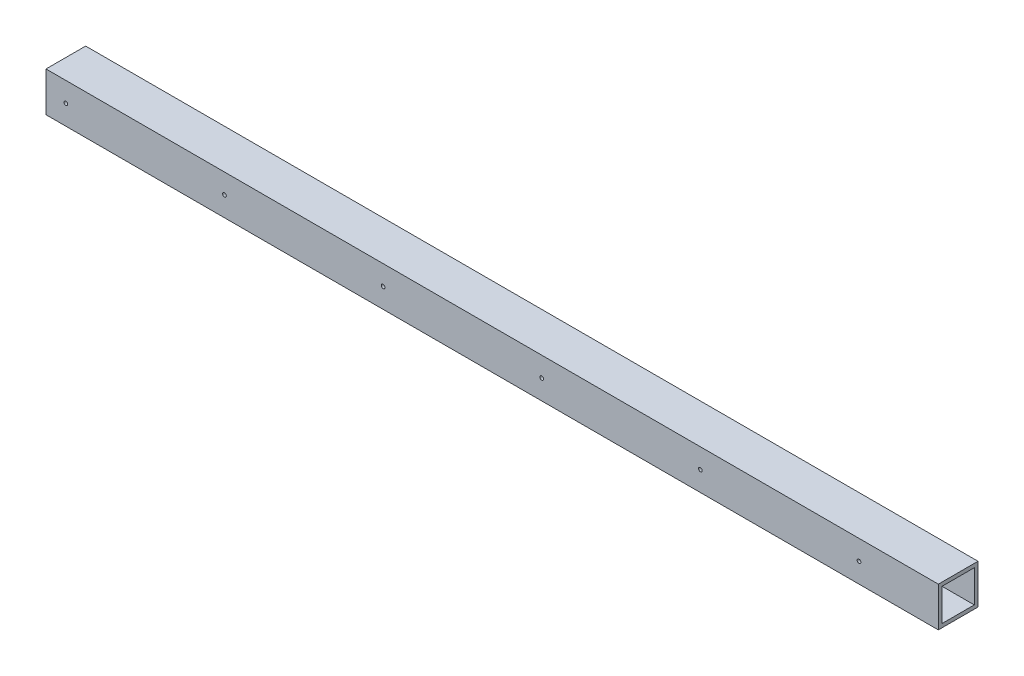
SolidWorks part; units mm, degrees
ref_plane "Front Plane" through (0, 0, 0) normal (0, 0, 1) x (1, 0, 0)
ref_plane "Top Plane" through (0, 0, 0) normal (0, 1, 0) x (1, 0, 0)
ref_plane "Right Plane" through (0, 0, 0) normal (1, 0, 0) x (0, 0, -1)
sketch "Sketch1" plane through (0, 0, 0) normal (1, 0, 0) x (0, 0, -1)
  line L0 (4.7625, 4.7625) -> (4.7625, 46.0375)
  line L1 (0, 0) -> (50.8, 0)
  line L2 (0, 0) -> (0, 50.8)
  line L3 (0, 50.8) -> (50.8, 50.8)
  line L4 (50.8, 0) -> (50.8, 50.8)
  line L5 (4.7625, 46.0375) -> (46.0375, 46.0375)
  line L6 (46.0375, 4.7625) -> (46.0375, 46.0375)
  line L7 (4.7625, 4.7625) -> (46.0375, 4.7625)
  dimension "D1" = 50.8
  dimension "D2" = 4.7625
extrude "Boss-Extrude1" add sketch "Sketch1" along normal blind 1143
sketch "Sketch2" plane through (0, 0, -50.8) normal (0, 0, -1) x (-1, 0, 0)
  line L0 (-1143, 0) -> (-1143, 50.8) construction
  line L1 (-1143, 50.8) -> (0, 50.8) construction
  circle A0 centre (-1041.4, 25.4) radius 2.3813
  dimension "D3" = 4.7625
  dimension "D1" = 101.6
  dimension "D2" = 25.4
extrude "Cut-Extrude1" cut sketch "Sketch2" against normal through all
pattern_linear "LPattern1" count 6 spacing 203.2 along (-1, 0, 0) of "Cut-Extrude1"
sketch "Sketch3" plane through (0, 0, 0) normal (0, -1, 0) x (1, 0, 0)
  line L0 (0, 0) -> (0, -50.8) construction
  circle A0 centre (101.6, -25.4) radius 2.3813
  point P5 (0, -25.4)
  dimension "D1" = 101.6
  dimension "D2" = 4.7625
extrude "Cut-Extrude2" cut sketch "Sketch3" against normal up to surface (4.7625 mm away) up to face at (571.5, 4.7625, -25.4)
pattern_linear "LPattern2" count 6 spacing 203.2 along (1, 0, 0) of "Cut-Extrude2"
